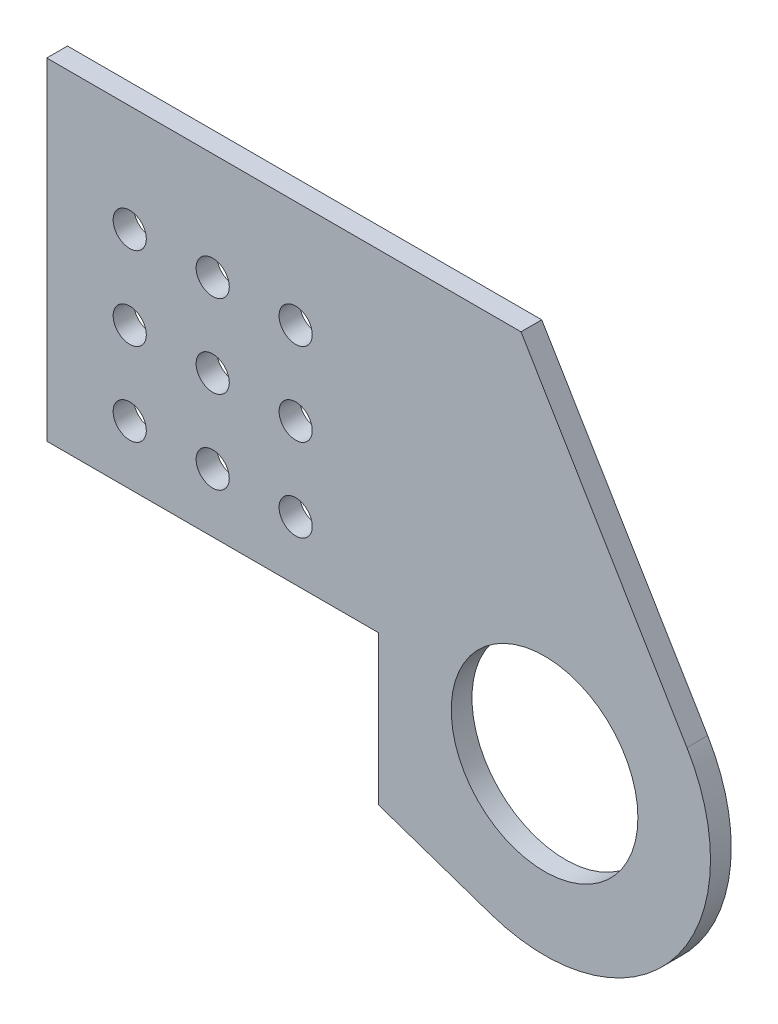
SolidWorks part; units mm, degrees
ref_plane "Front Plane" through (0, 0, 0) normal (0, 0, 1) x (1, 0, 0)
ref_plane "Top Plane" through (0, 0, 0) normal (0, 1, 0) x (1, 0, 0)
ref_plane "Right Plane" through (0, 0, 0) normal (1, 0, 0) x (0, 0, -1)
sketch "Sketch1" plane through (0, 0, 0) normal (0, 0, 1) x (1, 0, 0)
  line L0 (0, 0) -> (0, 50.8)
  line L4 (0, 50.8) -> (72.5919, 50.8)
  line L7 (72.5919, 50.8) -> (97.9919, 8.3811)
  line L8 (67.9855, -28.7027) -> (50.8, -22.8292)
  line L10 (0, 0) -> (50.8, 0)
  line L16 (50.8, 0) -> (50.8, -22.8292)
  arc A0 (97.9919, 8.3811) -> (67.9855, -28.7027) centre (76.2, -4.6677) cw
  circle A1 centre (12.7, 34.4279) radius 2.54
  circle A2 centre (25.4, 34.4279) radius 2.54
  circle A3 centre (38.1, 34.4279) radius 2.54
  circle A4 centre (25.4, 21.7279) radius 2.54
  circle A5 centre (38.1, 21.7279) radius 2.54
  circle A6 centre (25.4, 9.0279) radius 2.54
  circle A7 centre (38.1, 9.0279) radius 2.54
  circle A8 centre (12.7, 21.7279) radius 2.54
  circle A9 centre (12.7, 9.0279) radius 2.54
  circle A10 centre (76.2, -4.6677) radius 14.2875
  circle A17 centre (12.573, 29.845) radius 4.5847 construction
  point P3 (50.8, 52.5617)
  point P27 (0, 0)
  point P28 (0, 0)
  point P29 (74.8947, 45.9102)
  point P31 (0, 0)
  point P33 (0, 0)
  dimension "D3" = 5.08
  dimension "D10" = 28.575
  dimension "D2" = 25.4
  dimension "D5" = 25.4
  dimension "D1" = 50.8
  dimension "D4" = 12.7
  dimension "D8" = 12.7
  dimension "D9" = 12.7
  dimension "D11" = 22.8292
  dimension "D12" = 18.1615
  dimension "D13" = 25.4
  dimension "D14" = 50.8
  dimension "D6" = 3
  dimension "D7" = 3
extrude "Boss-Extrude1" add sketch "Sketch1" along normal blind 3.175
